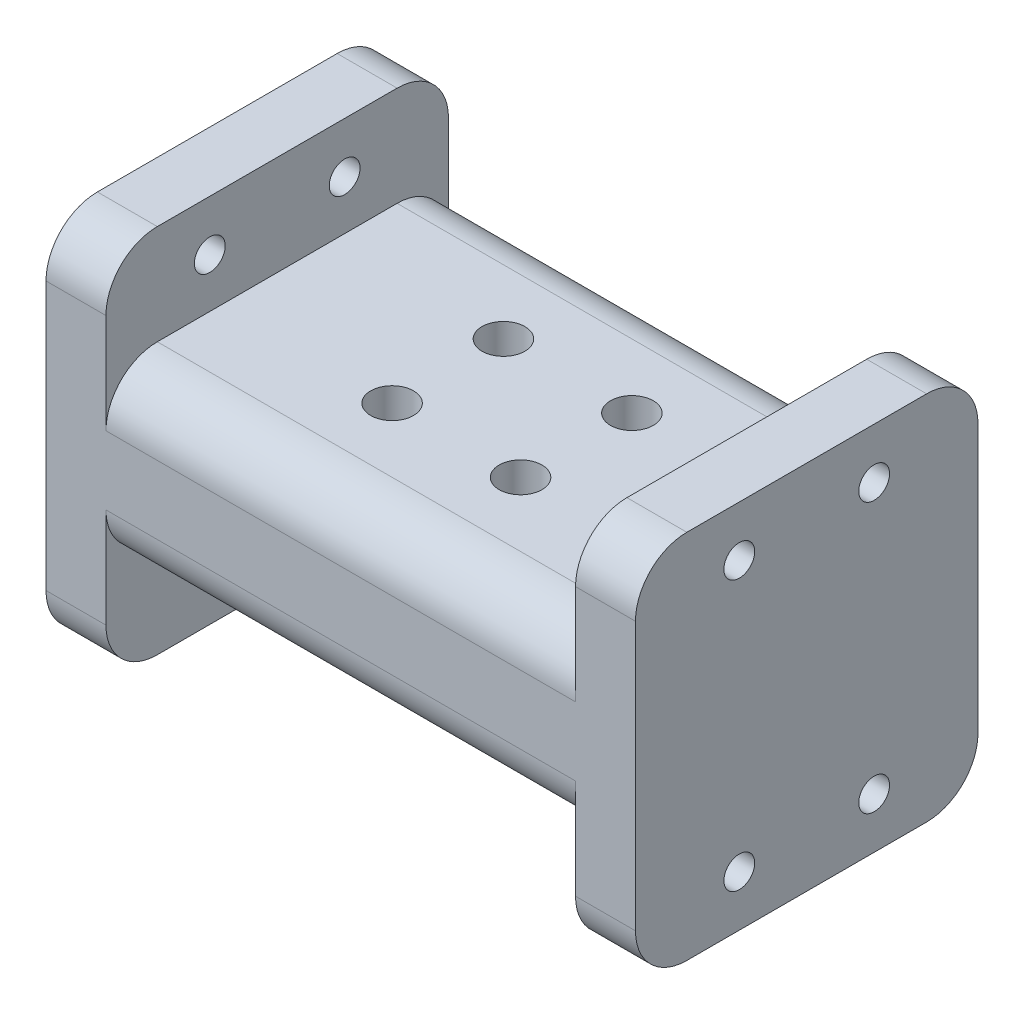
SolidWorks part; units mm, degrees
ref_plane "Front Plane" through (0, 0, 0) normal (0, 0, 1) x (1, 0, 0)
ref_plane "Top Plane" through (0, 0, 0) normal (0, 1, 0) x (1, 0, 0)
ref_plane "Right Plane" through (0, 0, 0) normal (1, 0, 0) x (0, 0, -1)
sketch "Sketch1" plane through (0, 0, 0) normal (1, 0, 0) x (0, 0, -1)
  line L0 (10, 20) -> (-10, 20) construction
  line L1 (-25.4, 27.5) -> (25.4, 27.5)
  line L2 (-25.4, 27.5) -> (-25.4, -27.5)
  line L3 (-25.4, -27.5) -> (25.4, -27.5)
  line L4 (25.4, 27.5) -> (25.4, -27.5)
  line L5 (-10, -20) -> (10, -20) construction
  line L6 (0, 20) -> (0, -20) construction
  circle A0 centre (-10, 20) radius 2.286
  circle A1 centre (10, 20) radius 2.286
  circle A2 centre (-10, -20) radius 2.286
  circle A3 centre (10, -20) radius 2.286
  point P4 (0, 27.5)
  point P6 (25.4, 0)
  point P17 (0, 0)
  dimension "D7" = 4.572
  dimension "D1" = 50.8
  dimension "D2" = 55
  dimension "D3" = 40
  dimension "D4" = 20
extrude "Boss-Extrude1" add sketch "Sketch1" along normal blind 8.89
fillet "Fillet1" radius 7.62 4 edges at (4.445, 27.5, -25.4) (4.445, -27.5, -25.4) (4.445, -27.5, 25.4) (4.445, 27.5, 25.4)
sketch "Sketch2" plane through (8.89, 0, 0) normal (1, 0, 0) x (0, 0, -1)
  line L0 (-25.4, 19.88) -> (-25.4, -19.88) construction
  line L1 (-25.4, 12.7) -> (25.4, 12.7)
  line L2 (-25.4, 12.7) -> (-25.4, -12.7)
  line L3 (-25.4, -12.7) -> (25.4, -12.7)
  line L4 (25.4, 12.7) -> (25.4, -12.7)
  line L5 (25.4, -19.88) -> (25.4, 19.88) construction
  point P8 (25.4, 0)
  dimension "D1" = 25.4
extrude "Boss-Extrude2" add sketch "Sketch2" along normal blind 34.8196
fillet "Fillet2" radius 7.62 4 edges at (26.2998, -12.7, -25.4) (26.2998, 12.7, -25.4) (26.2998, -12.7, 25.4) (26.2998, 12.7, 25.4)
mirror "Mirror6" about plane through (43.7096, 0, 0) normal (1, 0, 0) of bodies 105
sketch "Sketch3" plane through (0, 12.7, 0) normal (0, 1, 0) x (1, 0, 0)
  line L0 (34.1846, 8.255) -> (53.2346, 8.255) construction
  line L2 (8.89, -17.78) -> (78.5292, -17.78) construction
  circle A0 centre (53.2346, 8.255) radius 3.175
  circle A1 centre (34.1846, 8.255) radius 3.175
  point P4 (43.7096, 8.255)
  point P9 (43.7096, -17.78)
  dimension "D2" = 6.35
  dimension "D1" = 19.05
  dimension "D3" = 8.255
extrude "Cut-Extrude1" cut sketch "Sketch3" against normal through all
pattern_linear "LPattern1" count 2 spacing 16.51 along (0, 0, 1) of "Cut-Extrude1"
